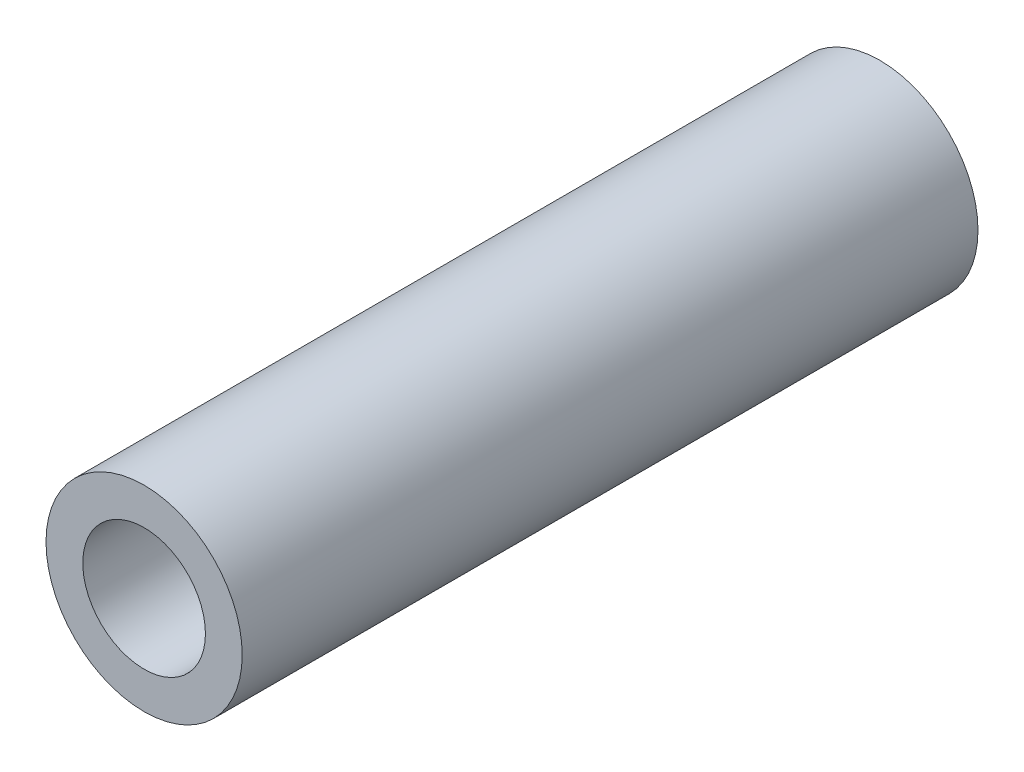
SolidWorks part; units mm, degrees
material "Brass"
ref_plane "Front Plane" through (0, 0, 0) normal (0, 0, 1) x (1, 0, 0)
ref_plane "Top Plane" through (0, 0, 0) normal (0, 1, 0) x (1, 0, 0)
ref_plane "Right Plane" through (0, 0, 0) normal (1, 0, 0) x (0, 0, -1)
sketch "Sketch1" plane through (0, 0, 0) normal (0, 0, 1) x (1, 0, 0)
  circle A0 centre (0, 0) radius 1.6
  circle A1 centre (0, 0) radius 1
  dimension "D1" = 3.2
  dimension "D2" = 2
extrude "Boss-Extrude1" add sketch "Sketch1" along normal blind 12
ref_point "Point1"
